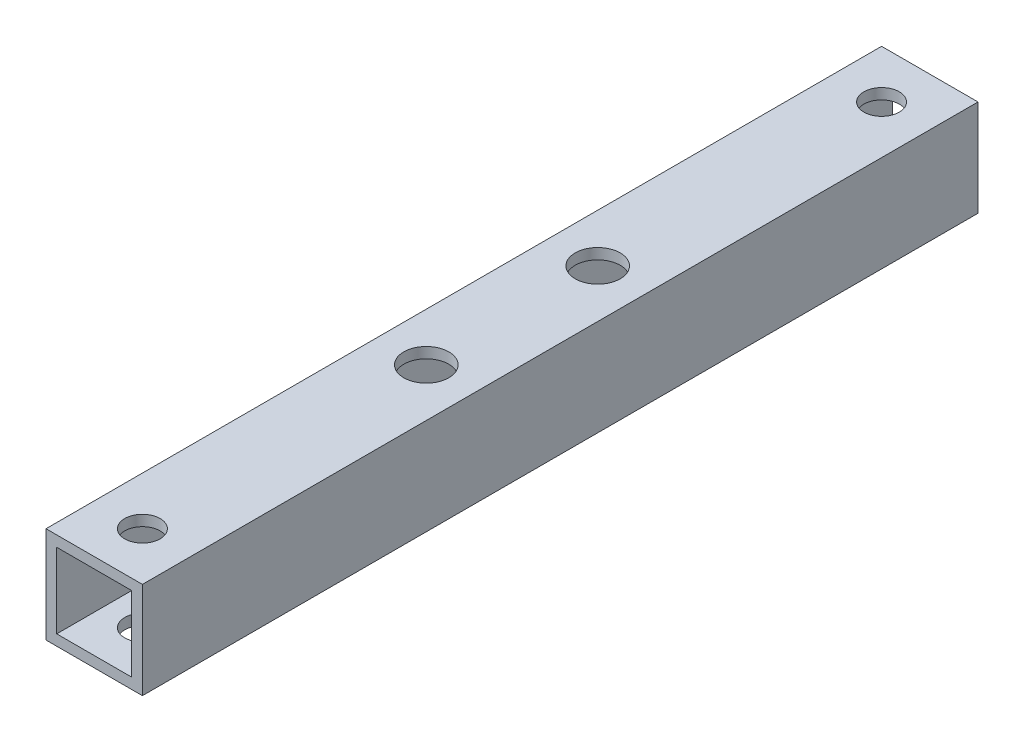
SolidWorks part; units mm, degrees
ref_plane "正面" through (0, 0, 0) normal (0, 0, 1) x (1, 0, 0)
ref_plane "平面" through (0, 0, 0) normal (0, 1, 0) x (1, 0, 0)
ref_plane "右側面" through (0, 0, 0) normal (1, 0, 0) x (0, 0, -1)
sketch "ｽｹｯﾁ1" plane through (0, 0, 0) normal (0, 0, 1) x (1, 0, 0)
  line L1 (-4.5, 4.5) -> (4.5, 4.5)
  line L2 (-4.5, 4.5) -> (-4.5, -4.5)
  line L3 (-4.5, -4.5) -> (4.5, -4.5)
  line L4 (4.5, 4.5) -> (4.5, -4.5)
  line L5 (-4.5, 4.5) -> (4.5, -4.5) construction
  line L6 (-4.5, -4.5) -> (4.5, 4.5) construction
  point P0 (0, 0)
  dimension "D1" = 9
  dimension "D2" = 9
extrude "ﾎﾞｽ - 押し出し1" add sketch "ｽｹｯﾁ1" along normal blind 78
sketch "ｽｹｯﾁ2" plane through (0, 0, 78) normal (0, 0, 1) x (1, 0, 0)
  line L1 (-3.5, 3.5) -> (3.5, 3.5)
  line L2 (-3.5, 3.5) -> (-3.5, -3.5)
  line L3 (-3.5, -3.5) -> (3.5, -3.5)
  line L4 (3.5, 3.5) -> (3.5, -3.5)
  line L5 (-3.5, 3.5) -> (3.5, -3.5) construction
  line L6 (-3.5, -3.5) -> (3.5, 3.5) construction
  point P0 (0, 0)
  dimension "D1" = 7
  dimension "D2" = 7
extrude "ｶｯﾄ - 押し出し1" cut sketch "ｽｹｯﾁ2" against normal blind 90
sketch "ｽｹｯﾁ3" plane through (0, 4.5, 0) normal (0, 1, 0) x (1, 0, 0)
  line L0 (0, 0) -> (0, -4.5)
  line L1 (0, -78) -> (0, -73.5)
  line L2 (4.5, -78) -> (-4.5, -78) construction
  circle A0 centre (0, -4.5) radius 1.65
  circle A1 centre (0, -73.5) radius 1.65
  dimension "D2" = 3.3
  dimension "D3" = 3.3
  dimension "D1" = 4.5
  dimension "D4" = 4.5
extrude "ｶｯﾄ - 押し出し2" cut sketch "ｽｹｯﾁ3" against normal blind 75
sketch "ｽｹｯﾁ4" plane through (0, 4.5, 0) normal (0, 1, 0) x (1, 0, 0)
  line L0 (0, 0) -> (0, -31)
  line L1 (0, -78) -> (0, -47)
  line L2 (4.5, -78) -> (-4.5, -78) construction
  circle A0 centre (0, -31) radius 2.1
  circle A1 centre (0, -47) radius 2.1
  dimension "D3" = 4.2
  dimension "D4" = 4.2
  dimension "D1" = 31
  dimension "D2" = 31
extrude "ｶｯﾄ - 押し出し3" cut sketch "ｽｹｯﾁ4" against normal blind 75
